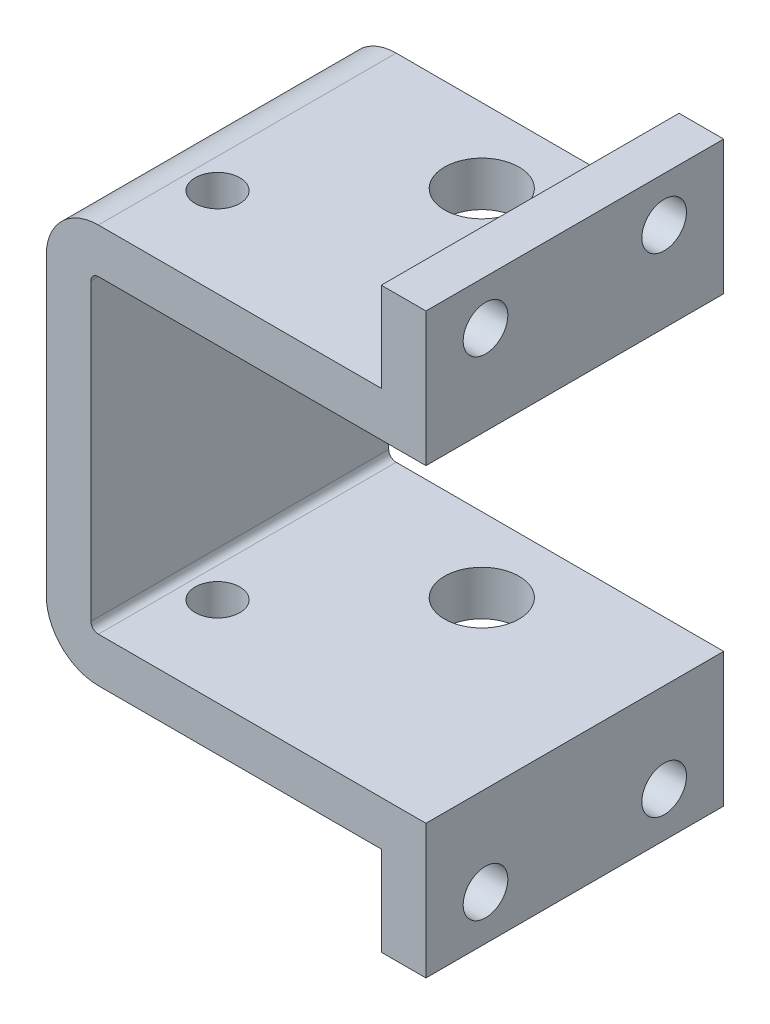
SolidWorks part; units mm, degrees
ref_plane "Front Plane" through (0, 0, 0) normal (0, 0, 1) x (1, 0, 0)
ref_plane "Top Plane" through (0, 0, 0) normal (0, 1, 0) x (1, 0, 0)
ref_plane "Right Plane" through (0, 0, 0) normal (1, 0, 0) x (0, 0, -1)
sketch "Sketch1" plane through (0, 0, 0) normal (0, 0, 1) x (1, 0, 0)
  line L0 (-1.0167, -10.4) -> (20.9833, -10.4)
  line L1 (-1.5167, -9.9) -> (-1.5167, 9.9)
  line L2 (-1.0167, 10.4) -> (20.9833, 10.4)
  line L3 (17.9833, 19.4) -> (17.9833, 13.4)
  line L4 (0, -9.4) -> (0, 9.4) construction
  line L5 (0, 0) -> (-3.0334, 0) construction
  line L6 (-4.5167, -9.9) -> (-4.5167, 9.9)
  line L7 (-1.0167, 13.4) -> (17.9833, 13.4)
  line L8 (20.9833, 19.4) -> (17.9833, 19.4)
  line L9 (-1.0167, -13.4) -> (17.9833, -13.4)
  line L10 (20.9833, -10.4) -> (20.9833, -19.4)
  line L11 (20.9833, -19.4) -> (17.9833, -19.4)
  line L12 (17.9833, -19.4) -> (17.9833, -13.4)
  line L13 (20.9833, 10.4) -> (20.9833, 19.4)
  arc A0 (-1.5167, 9.9) -> (-1.0167, 10.4) centre (-1.0167, 9.9) cw
  arc A1 (-1.0167, -10.4) -> (-1.5167, -9.9) centre (-1.0167, -9.9) cw
  arc A2 (-4.5167, 9.9) -> (-1.0167, 13.4) centre (-1.0167, 9.9) cw
  arc A3 (-1.0167, -13.4) -> (-4.5167, -9.9) centre (-1.0167, -9.9) cw
  point P8 (-1.5167, 0)
  dimension "D1" = 0.5
  dimension "D2" = 3
  dimension "D3" = 6
extrude "Boss-Extrude1" add sketch "Sketch1" along normal blind 20
sketch "Sketch2" plane through (0, 13.4, 0) normal (0, 1, 0) x (1, 0, 0)
  line L0 (-1.5167, -14) -> (20.9833, -14) construction
  line L1 (-1.5167, -20) -> (-1.5167, 0) construction
  line L2 (-4.5167, -20) -> (-1.0167, -20) construction
  line L3 (20.9833, -20) -> (20.9833, 0) construction
  line L4 (9.7333, -20) -> (9.7333, 0) construction
  line L5 (17.9833, -20) -> (-1.0167, -20) construction
  line L6 (17.9833, 0) -> (-1.0167, 0) construction
  circle A0 centre (0.9833, -14) radius 1.5
  circle A1 centre (9.7333, -5) radius 2.5
  point P6 (0.9833, -14)
  point P19 (9.7333, -7.5)
  dimension "D3" = 3
  dimension "D4" = 5
  dimension "D1" = 6
  dimension "D2" = 2.5
  dimension "D5" = 12.5
extrude "Cut-Extrude1" cut sketch "Sketch2" against normal blind 27
sketch "Sketch3" plane through (17.9833, 0, 0) normal (-1, 0, 0) x (0, 0, 1)
  line L0 (20, 16.4) -> (0, 16.4) construction
  line L1 (20, 19.4) -> (20, 13.4) construction
  line L2 (0, 19.4) -> (0, 13.4) construction
  line L3 (10, 13.4) -> (10, 19.4) construction
  line L4 (20, 13.4) -> (0, 13.4) construction
  line L5 (20, 19.4) -> (0, 19.4) construction
  line L6 (20, 0) -> (0, 0) construction
  line L7 (20, 9.9) -> (20, -9.9) construction
  line L8 (10, -13.4) -> (10, -19.4) construction
  line L9 (20, -16.4) -> (0, -16.4) construction
  circle A0 centre (16, 16.4) radius 1.5
  circle A1 centre (4, 16.4) radius 1.5
  circle A2 centre (4, -16.4) radius 1.5
  circle A3 centre (16, -16.4) radius 1.5
  dimension "D1" = 3
  dimension "D2" = 4
extrude "Cut-Extrude2" cut sketch "Sketch3" against normal blind 27
